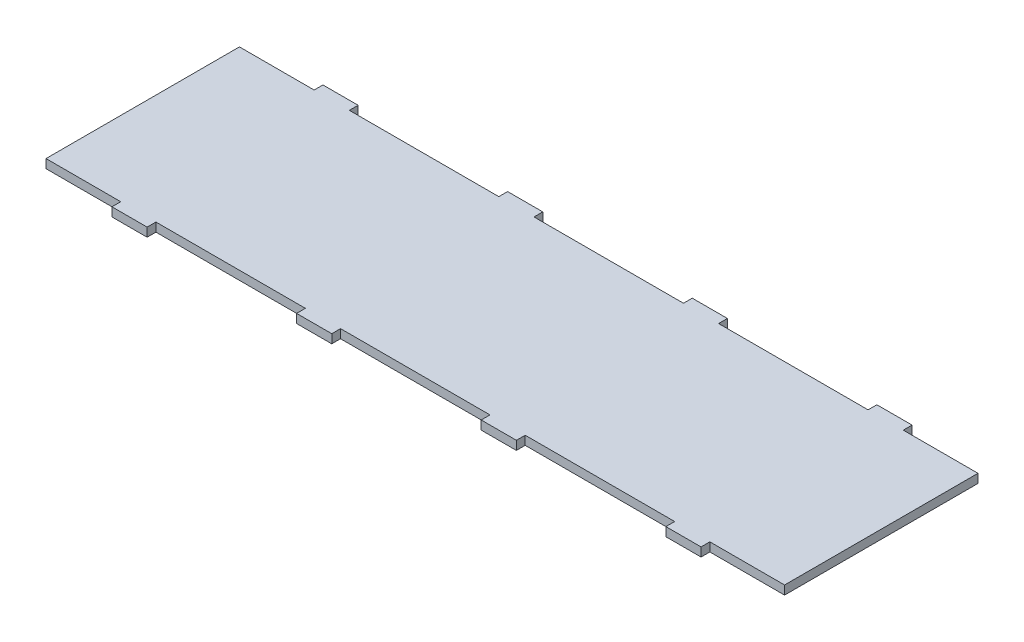
SolidWorks part; units mm, degrees
material "Cedar"
ref_plane "Front Plane" through (0, 0, 0) normal (0, 0, 1) x (1, 0, 0)
ref_plane "Top Plane" through (0, 0, 0) normal (0, 1, 0) x (1, 0, 0)
ref_plane "Right Plane" through (0, 0, 0) normal (1, 0, 0) x (0, 0, -1)
sketch "Sketch1" plane through (0, 0, 0) normal (0, 1, 0) x (1, 0, 0)
  line L1 (-266.7, 76.2) -> (266.7, 76.2)
  line L2 (-266.7, 76.2) -> (-266.7, -76.2)
  line L3 (-266.7, -76.2) -> (266.7, -76.2)
  line L4 (266.7, 76.2) -> (266.7, -76.2)
  line L5 (-266.7, 76.2) -> (266.7, -76.2) construction
  line L6 (-266.7, -76.2) -> (266.7, 76.2) construction
  point P0 (0, 0)
  point P5 (0, 0)
  dimension "D1" = 152.4
  dimension "D2" = 533.4
extrude "Boss-Extrude1" add sketch "Sketch1" along normal blind 6.35
sketch "Sketch2" plane through (0, 6.35, 0) normal (0, 1, 0) x (1, 0, 0)
  line L0 (-266.7, -69.85) -> (266.7, -69.85) construction
  line L1 (-266.7, 76.2) -> (-266.7, -76.2) construction
  line L2 (266.7, -76.2) -> (266.7, 76.2) construction
  line L3 (-266.7, -76.2) -> (266.7, -76.2) construction
  line L5 (-53.975, -69.85) -> (53.975, -69.85)
  line L6 (-53.975, -69.85) -> (-53.975, -76.2)
  line L7 (-53.975, -76.2) -> (53.975, -76.2)
  line L8 (53.975, -69.85) -> (53.975, -76.2)
  line L9 (-53.975, -69.85) -> (53.975, -76.2) construction
  line L10 (-53.975, -76.2) -> (53.975, -69.85) construction
  point P8 (0, -73.025)
  point P13 (0, 0)
  point P14 (0, -69.85)
  point P15 (-39.2329, -76.2)
  point P16 (0, 0)
  point P17 (0, 0)
  point P18 (0, -69.85)
  dimension "D1" = 6.35
  dimension "D2" = 107.95
extrude "Cut-Extrude2" cut sketch "Sketch2" against normal through all
pattern_linear "LPattern1" count 3 spacing 133.35 along (-1, 0, 0) count 3 spacing 133.35 along (1, 0, 0) of "Cut-Extrude2"
mirror "Mirror2" about plane through (0, 0, 0) normal (0, 0, 1) of "LPattern1", "Cut-Extrude2"
